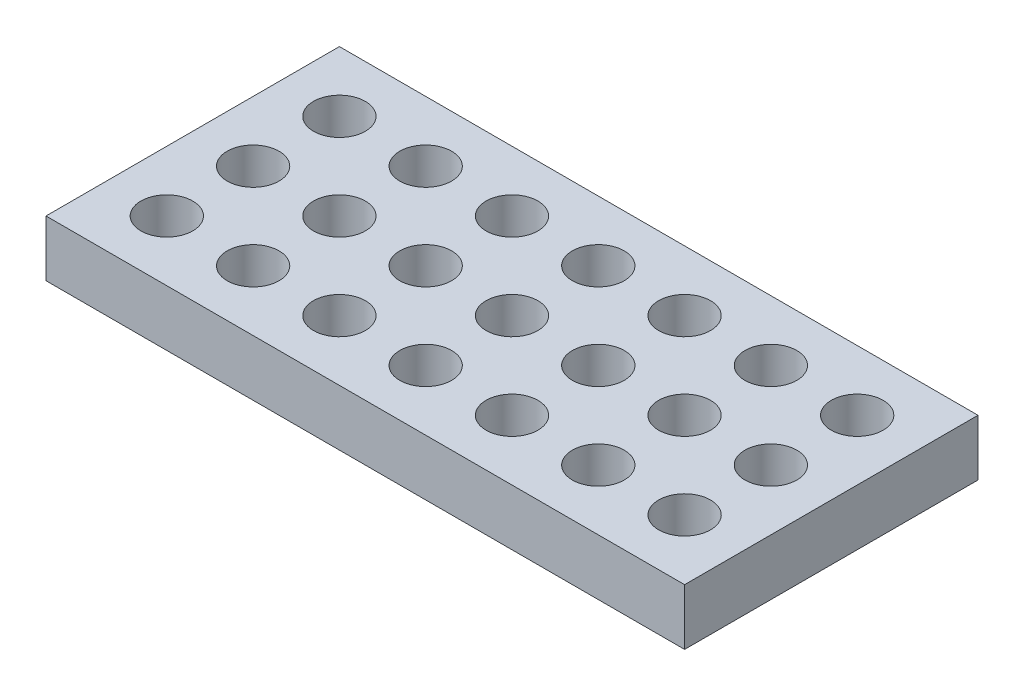
SolidWorks part; units mm, degrees
material "ABS"
ref_plane "Front Plane" through (0, 0, 0) normal (0, 0, 1) x (1, 0, 0)
ref_plane "Top Plane" through (0, 0, 0) normal (0, 1, 0) x (1, 0, 0)
ref_plane "Right Plane" through (0, 0, 0) normal (1, 0, 0) x (0, 0, -1)
sketch "Sketch1" plane through (0, 0, 0) normal (0, 1, 0) x (1, 0, 0)
  line L0 (-18.5, 8.5) -> (18.5, -8.5) construction
  line L1 (-18.5, 8.5) -> (18.5, 8.5)
  line L2 (-18.5, 8.5) -> (-18.5, -8.5)
  line L3 (-18.5, -8.5) -> (18.5, -8.5)
  line L4 (18.5, 8.5) -> (18.5, -8.5)
  circle A0 centre (-15, -5) radius 1.5025
  circle A1 centre (-10, -5) radius 1.5025
  circle A2 centre (-5, -5) radius 1.5025
  circle A3 centre (0, -5) radius 1.5025
  circle A4 centre (5, -5) radius 1.5025
  circle A5 centre (10, -5) radius 1.5025
  circle A6 centre (15, -5) radius 1.5025
  circle A7 centre (-10, 0) radius 1.5025
  circle A8 centre (-5, 0) radius 1.5025
  circle A9 centre (0, 0) radius 1.5025
  circle A10 centre (5, 0) radius 1.5025
  circle A11 centre (10, 0) radius 1.5025
  circle A12 centre (15, 0) radius 1.5025
  circle A13 centre (-10, 5) radius 1.5025
  circle A14 centre (-5, 5) radius 1.5025
  circle A15 centre (0, 5) radius 1.5025
  circle A16 centre (5, 5) radius 1.5025
  circle A17 centre (10, 5) radius 1.5025
  circle A18 centre (15, 5) radius 1.5025
  circle A19 centre (-15, 0) radius 1.5025
  circle A20 centre (-15, 5) radius 1.5025
  dimension "D5" = 3.005
  dimension "D8" = 3.5
  dimension "D9" = 3.5
  dimension "D1" = 37
  dimension "D2" = 17
  dimension "D3" = 3.5
  dimension "D4" = 3.5
  dimension "D10" = 3.5
  dimension "D11" = 3.5
  dimension "D6" = 7
  dimension "D7" = 3
extrude "Boss-Extrude1" add sketch "Sketch1" along normal blind 3.25
